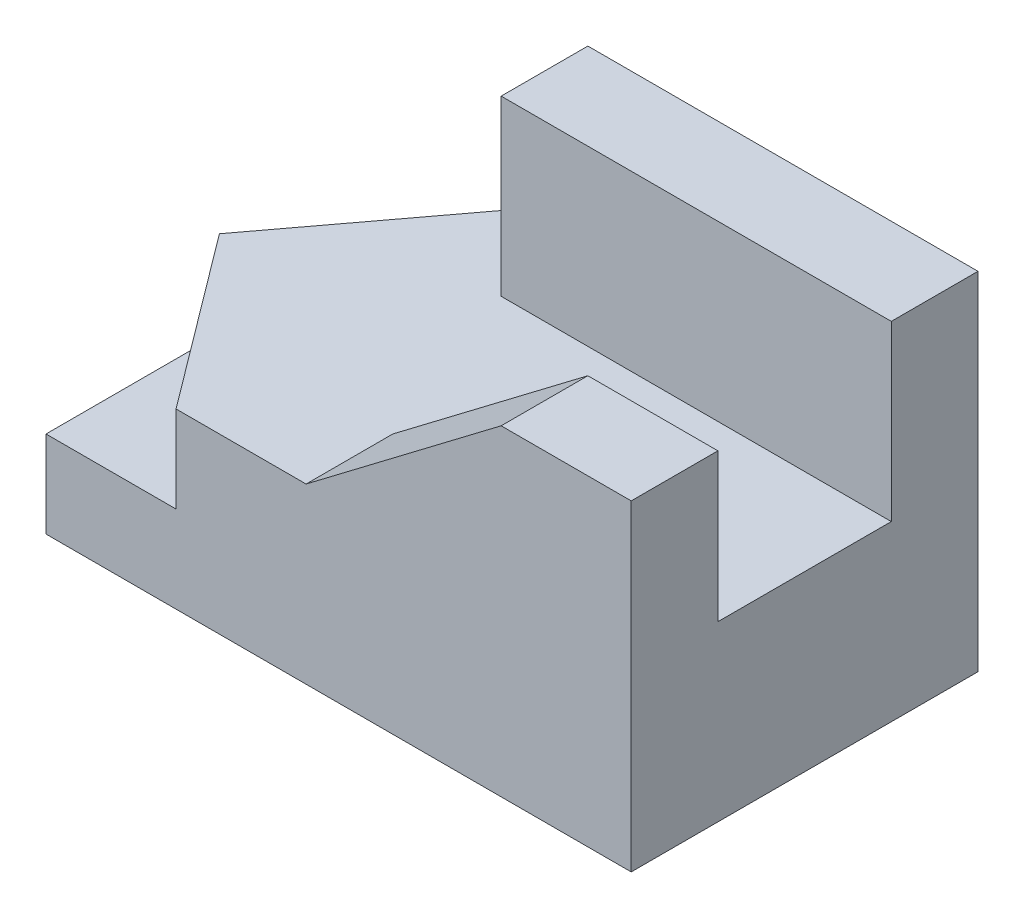
SolidWorks part; units mm, degrees
ref_plane "Front" through (0, 0, 0) normal (0, 0, 1) x (1, 0, 0)
ref_plane "Top" through (0, 0, 0) normal (0, 1, 0) x (1, 0, 0)
ref_plane "Right" through (0, 0, 0) normal (1, 0, 0) x (0, 0, -1)
sketch "Sketch1" plane through (0, 0, 0) normal (0, 1, 0) x (1, 0, 0)
  line L1 (-6.75, -4) -> (6.75, -4)
  line L2 (-6.75, -4) -> (-6.75, 4)
  line L3 (-6.75, 4) -> (6.75, 4)
  line L4 (6.75, -4) -> (6.75, 4)
  line L5 (-6.75, -4) -> (6.75, 4) construction
  line L6 (-6.75, 4) -> (6.75, -4) construction
  point P0 (0, 0)
  dimension "D1" = 13.5
  dimension "D2" = 8
extrude "Boss-Extrude1" add sketch "Sketch1" along normal blind 2
sketch "Sketch2" plane through (0, 2, 0) normal (0, 1, 0) x (1, 0, 0)
  line L0 (-6.75, 0) -> (-3.75, 4)
  line L1 (-6.75, 4) -> (-6.75, -4) construction
  line L2 (6.75, 4) -> (-6.75, 4) construction
  line L3 (-3.75, 4) -> (6.75, 4)
  line L4 (6.75, 4) -> (6.75, -4)
  line L5 (6.75, -4) -> (-3.75, -4)
  line L6 (-6.75, -4) -> (6.75, -4) construction
  line L7 (-3.75, -4) -> (-6.75, 0)
  dimension "D1" = 3
  dimension "D2" = 3
extrude "Boss-Extrude2" add sketch "Sketch2" along normal blind 2
sketch "Sketch3" plane through (0, 4, 0) normal (0, 1, 0) x (1, 0, 0)
  line L0 (-3.75, -4) -> (6.75, -4) construction
  line L1 (6.75, 4) -> (-2.25, 4)
  line L2 (6.75, 4) -> (6.75, 2)
  line L3 (6.75, 2) -> (-2.25, 2)
  line L4 (-2.25, 4) -> (-2.25, 2)
  line L5 (-0.75, -4) -> (6.75, -4)
  line L6 (-0.75, -4) -> (-0.75, -2)
  line L7 (-0.75, -2) -> (6.75, -2)
  line L8 (6.75, -4) -> (6.75, -2)
  line L9 (6.75, -4) -> (6.75, 4) construction
  dimension "D1" = 9
  dimension "D2" = 2
  dimension "D3" = 7.5
  dimension "D4" = 2
extrude "Boss-Extrude3" add sketch "Sketch3" along normal blind 4
sketch "Sketch4" plane through (0, 0, 4) normal (0, 0, 1) x (1, 0, 0)
  line L0 (6.75, 7.4134) -> (3.75, 7.4134)
  line L1 (6.75, 8) -> (6.75, 0) construction
  line L2 (3.75, 7.4134) -> (-0.75, 4)
  line L4 (-0.75, 4) -> (-0.75, 8)
  line L5 (-0.75, 8) -> (6.75, 8)
  line L6 (6.75, 8) -> (6.75, 7.4134)
  point P6 (0, 0)
  point P12 (-0.75, 4)
  point P14 (-0.8505, 4)
  dimension "D1" = 3
extrude "Cut-Extrude1" cut sketch "Sketch4" against normal blind 4
